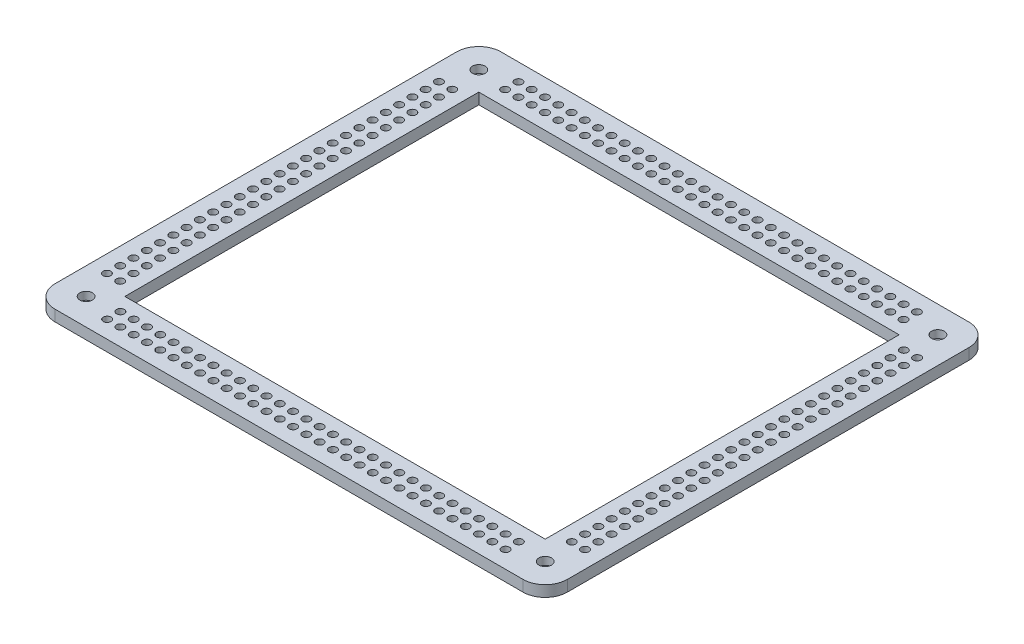
SolidWorks part; units mm, degrees
ref_plane "Front Plane" through (0, 0, 0) normal (0, 0, 1) x (1, 0, 0)
ref_plane "Top Plane" through (0, 0, 0) normal (0, 1, 0) x (1, 0, 0)
ref_plane "Right Plane" through (0, 0, 0) normal (1, 0, 0) x (0, 0, -1)
sketch "Sketch1" plane through (0, 0, 0) normal (0, 1, 0) x (1, 0, 0)
  line L1 (-94.95, 79.95) -> (94.95, 79.95)
  line L2 (-94.95, 79.95) -> (-94.95, -79.95)
  line L3 (-94.95, -79.95) -> (94.95, -79.95)
  line L4 (94.95, 79.95) -> (94.95, -79.95)
  line L5 (-115.7, 100.7) -> (115.7, 100.7)
  line L6 (-115.7, 100.7) -> (-115.7, -100.7)
  line L7 (-115.7, -100.7) -> (115.7, -100.7)
  line L8 (115.7, 100.7) -> (115.7, -100.7)
  point P4 (-94.95, 0)
  point P6 (0, 79.95)
  point P11 (0, -100.7)
  point P12 (-115.7, 0)
  dimension "D1" = 189.9
  dimension "D2" = 159.9
  dimension "D3" = 20.75
  dimension "D4" = 20.75
extrude "Boss-Extrude1" add sketch "Sketch1" along normal blind 5
fillet "Fillet1" radius 10 4 edges at (-115.7, 2.5, -100.7) (115.7, 2.5, -100.7) (115.7, 2.5, 100.7) (-115.7, 2.5, 100.7)
sketch "Sketch2" plane through (0, 0, 0) normal (0, -1, 0) x (1, 0, 0)
  line L0 (-105.7, 100.7) -> (105.7, 100.7) construction
  line L1 (-115.7, -90.7) -> (-115.7, 90.7) construction
  circle A0 centre (-103.7, 88.7) radius 5.85
  dimension "D3" = 11.7
  dimension "D1" = 12
  dimension "D2" = 12
extrude "Boss-Extrude2" add sketch "Sketch2" along normal blind 2.5
sketch "Sketch3" plane through (0, 5, 0) normal (0, 1, 0) x (1, 0, 0)
  line L2 (-115.7, 90.7) -> (-115.7, -90.7) construction
  line L3 (-105.7, -100.7) -> (105.7, -100.7) construction
  circle A0 centre (-103.7, -88.7) radius 1.55
  dimension "D1" = 3.1
  dimension "D2" = 12
  dimension "D3" = 12
extrude "Cut-Extrude1" cut sketch "Sketch3" against normal blind 7.5
sketch "Sketch4" plane through (0, 5, 0) normal (0, 1, 0) x (1, 0, 0)
  circle A0 centre (-103.7, -88.7) radius 2.85
  dimension "D1" = 5.7
extrude "Cut-Extrude2" cut sketch "Sketch4" against normal blind 3.5
mirror "Mirror3" about plane through (0, 0, 0) normal (1, 0, 0) of "Cut-Extrude1", "Cut-Extrude2", "Boss-Extrude2"
mirror "Mirror4" about plane through (0, 0, 0) normal (0, 0, 1) of "Mirror3", "Boss-Extrude2", "Cut-Extrude1", "Cut-Extrude2"
sketch "Sketch5" plane through (0, 5, 0) normal (0, 1, 0) x (1, 0, 0)
  line L0 (-94.95, -79.95) -> (94.95, -79.95) construction
  line L1 (-115.7, 90.7) -> (-115.7, -90.7) construction
  circle A0 centre (-90, -86.9) radius 1.75
  circle A1 centre (-90, -92.9) radius 1.75
  circle A4 centre (-84, -86.9) radius 1.75
  circle A5 centre (-84, -92.9) radius 1.75
  circle A7 centre (-78, -86.9) radius 1.75
  circle A8 centre (-78, -92.9) radius 1.75
  circle A10 centre (-72, -86.9) radius 1.75
  circle A11 centre (-72, -92.9) radius 1.75
  circle A13 centre (-66, -86.9) radius 1.75
  circle A14 centre (-66, -92.9) radius 1.75
  circle A16 centre (-60, -86.9) radius 1.75
  circle A17 centre (-60, -92.9) radius 1.75
  circle A19 centre (-54, -86.9) radius 1.75
  circle A20 centre (-54, -92.9) radius 1.75
  circle A22 centre (-48, -86.9) radius 1.75
  circle A23 centre (-48, -92.9) radius 1.75
  circle A25 centre (-42, -86.9) radius 1.75
  circle A26 centre (-42, -92.9) radius 1.75
  circle A28 centre (-36, -86.9) radius 1.75
  circle A29 centre (-36, -92.9) radius 1.75
  circle A31 centre (-30, -86.9) radius 1.75
  circle A32 centre (-30, -92.9) radius 1.75
  circle A34 centre (-24, -86.9) radius 1.75
  circle A35 centre (-24, -92.9) radius 1.75
  circle A37 centre (-18, -86.9) radius 1.75
  circle A38 centre (-18, -92.9) radius 1.75
  circle A40 centre (-12, -86.9) radius 1.75
  circle A41 centre (-12, -92.9) radius 1.75
  circle A43 centre (-6, -86.9) radius 1.75
  circle A44 centre (-6, -92.9) radius 1.75
  circle A46 centre (0, -86.9) radius 1.75
  circle A47 centre (0, -92.9) radius 1.75
  circle A49 centre (6, -86.9) radius 1.75
  circle A50 centre (6, -92.9) radius 1.75
  circle A52 centre (12, -86.9) radius 1.75
  circle A53 centre (12, -92.9) radius 1.75
  circle A55 centre (18, -86.9) radius 1.75
  circle A56 centre (18, -92.9) radius 1.75
  circle A58 centre (24, -86.9) radius 1.75
  circle A59 centre (24, -92.9) radius 1.75
  circle A61 centre (30, -86.9) radius 1.75
  circle A62 centre (30, -92.9) radius 1.75
  circle A64 centre (36, -86.9) radius 1.75
  circle A65 centre (36, -92.9) radius 1.75
  circle A67 centre (42, -86.9) radius 1.75
  circle A68 centre (42, -92.9) radius 1.75
  circle A70 centre (48, -86.9) radius 1.75
  circle A71 centre (48, -92.9) radius 1.75
  circle A73 centre (54, -86.9) radius 1.75
  circle A74 centre (54, -92.9) radius 1.75
  circle A76 centre (60, -86.9) radius 1.75
  circle A77 centre (60, -92.9) radius 1.75
  circle A79 centre (66, -86.9) radius 1.75
  circle A80 centre (66, -92.9) radius 1.75
  circle A82 centre (72, -86.9) radius 1.75
  circle A83 centre (72, -92.9) radius 1.75
  circle A85 centre (78, -86.9) radius 1.75
  circle A86 centre (78, -92.9) radius 1.75
  circle A88 centre (84, -86.9) radius 1.75
  circle A89 centre (84, -92.9) radius 1.75
  circle A91 centre (90, -86.9) radius 1.75
  circle A92 centre (90, -92.9) radius 1.75
  circle A135 centre (108, -86.9) radius 1.75 [skipped]
  circle A136 centre (108, -92.9) radius 1.75 [skipped]
  circle A137 centre (102, -86.9) radius 1.75 [skipped]
  circle A138 centre (102, -92.9) radius 1.75 [skipped]
  circle A139 centre (96, -86.9) radius 1.75 [skipped]
  circle A140 centre (96, -92.9) radius 1.75 [skipped]
  dimension "D1" = 3.5
  dimension "D4" = 6
  dimension "D2" = 25.7
  dimension "D3" = 6
  dimension "D5" = 6.95
  dimension "D6" = 34
sketch "Sketch6" plane through (0, 5, 0) normal (0, 1, 0) x (1, 0, 0)
  line L1 (-115.7, 90.7) -> (-115.7, -90.7) construction
  circle A1 centre (-102, -75) radius 1.75
  circle A2 centre (-108, -75) radius 1.75
  circle A3 centre (-103.7, -88.7) radius 2.85 construction
  circle A5 centre (-102, -69) radius 1.75
  circle A6 centre (-108, -69) radius 1.75
  circle A8 centre (-102, -63) radius 1.75
  circle A9 centre (-108, -63) radius 1.75
  circle A11 centre (-102, -57) radius 1.75
  circle A12 centre (-108, -57) radius 1.75
  circle A14 centre (-102, -51) radius 1.75
  circle A15 centre (-108, -51) radius 1.75
  circle A17 centre (-102, -45) radius 1.75
  circle A18 centre (-108, -45) radius 1.75
  circle A20 centre (-102, -39) radius 1.75
  circle A21 centre (-108, -39) radius 1.75
  circle A23 centre (-102, -33) radius 1.75
  circle A24 centre (-108, -33) radius 1.75
  circle A26 centre (-102, -27) radius 1.75
  circle A27 centre (-108, -27) radius 1.75
  circle A29 centre (-102, -21) radius 1.75
  circle A30 centre (-108, -21) radius 1.75
  circle A32 centre (-102, -15) radius 1.75
  circle A33 centre (-108, -15) radius 1.75
  circle A35 centre (-102, -9) radius 1.75
  circle A36 centre (-108, -9) radius 1.75
  circle A38 centre (-102, -3) radius 1.75
  circle A39 centre (-108, -3) radius 1.75
  circle A41 centre (-102, 3) radius 1.75
  circle A42 centre (-108, 3) radius 1.75
  circle A44 centre (-102, 9) radius 1.75
  circle A45 centre (-108, 9) radius 1.75
  circle A47 centre (-102, 15) radius 1.75
  circle A48 centre (-108, 15) radius 1.75
  circle A50 centre (-102, 21) radius 1.75
  circle A51 centre (-108, 21) radius 1.75
  circle A53 centre (-102, 27) radius 1.75
  circle A54 centre (-108, 27) radius 1.75
  circle A56 centre (-102, 33) radius 1.75
  circle A57 centre (-108, 33) radius 1.75
  circle A59 centre (-102, 39) radius 1.75
  circle A60 centre (-108, 39) radius 1.75
  circle A62 centre (-102, 45) radius 1.75
  circle A63 centre (-108, 45) radius 1.75
  circle A65 centre (-102, 51) radius 1.75
  circle A66 centre (-108, 51) radius 1.75
  circle A68 centre (-102, 57) radius 1.75
  circle A69 centre (-108, 57) radius 1.75
  circle A71 centre (-102, 63) radius 1.75
  circle A72 centre (-108, 63) radius 1.75
  circle A74 centre (-102, 69) radius 1.75
  circle A75 centre (-108, 69) radius 1.75
  circle A77 centre (-102, 75) radius 1.75
  circle A78 centre (-108, 75) radius 1.75
  circle A116 centre (-102, 93) radius 1.75 [skipped]
  circle A117 centre (-108, 93) radius 1.75 [skipped]
  circle A118 centre (-102, 87) radius 1.75 [skipped]
  circle A119 centre (-108, 87) radius 1.75 [skipped]
  circle A120 centre (-102, 81) radius 1.75 [skipped]
  circle A121 centre (-108, 81) radius 1.75 [skipped]
  dimension "D4" = 13.7
  dimension "D1" = 7.7
  dimension "D2" = 6
  dimension "D7" = 29
extrude "Cut-Extrude3" cut sketch "Sketch5" against normal blind 10
extrude "Cut-Extrude4" cut sketch "Sketch6" against normal blind 10
mirror "Mirror5" about plane through (0, 0, 0) normal (0, 0, 1) of "Cut-Extrude3"
mirror "Mirror6" about plane through (0, 0, 0) normal (1, 0, 0) of "Cut-Extrude4"
